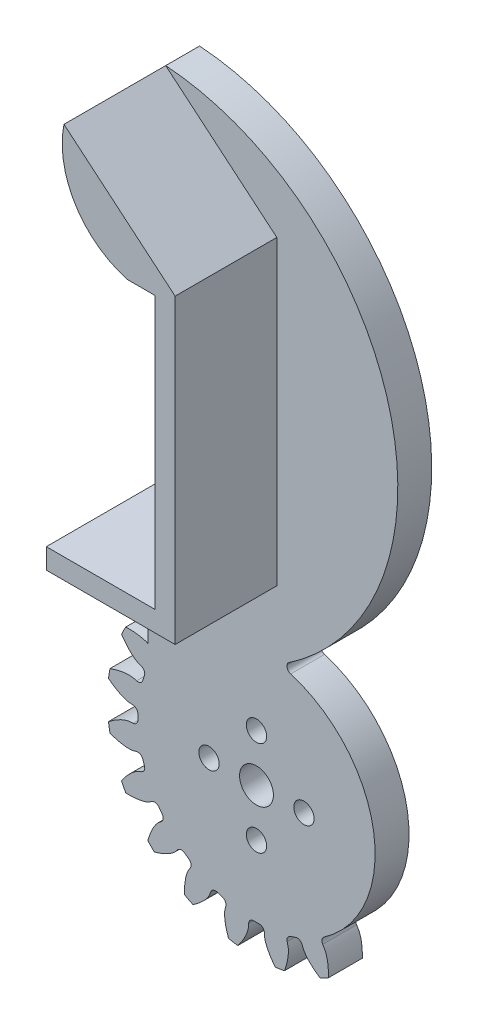
SolidWorks part; units mm, degrees
ref_plane "前视基准面" through (0, 0, 0) normal (0, 0, 1) x (1, 0, 0)
ref_plane "上视基准面" through (0, 0, 0) normal (0, 1, 0) x (1, 0, 0)
ref_plane "右视基准面" through (0, 0, 0) normal (1, 0, 0) x (0, 0, -1)
ref_axis "Axis1" through (0, 0, -88.99) along (0, 0, 1)
sketch "草图1" plane through (0, 0, 0) normal (0, 0, 1) x (1, 0, 0)
  circle A0 centre (0, 0) radius 22
extrude "LaShenA" add sketch "草图1" along normal blind 5
sketch "SketchA" plane through (0, 0, 5) normal (0, 0, 1) x (1, 0, 0)
  line L0 (0, 0) -> (0, 22) construction
  arc A0 (0.3853, 17.4958) -> (-0.3853, 17.4958) centre (0, 0) ccw
  arc A1 (3.5863, 22.7662) -> (-3.5863, 22.7662) centre (0, 0) ccw
  arc A2 (-0.3853, 17.4958) -> (-1.1606, 18.2089) centre (-0.4021, 18.2556) cw
  arc A3 (1.1606, 18.2089) -> (0.3853, 17.4958) centre (0.4021, 18.2556) cw
  circle A4 centre (0, 0) radius 18.7939 construction
  circle A5 centre (0, 0) radius 22 construction
  circle A6 centre (0, 0) radius 17.5 construction
  circle A7 centre (0, 0) radius 20 construction
  spline S0 degree 3 poles (1.1606, 18.2089) (1.1719, 18.3923) (1.1762, 18.6326) (1.2161, 18.8968) (1.2407, 19.0085) (1.2625, 19.0969) (1.2905, 19.1982) (1.3253, 19.3121) (1.3676, 19.4382) (1.4182, 19.5763) (1.4777, 19.7261) (1.5468, 19.887) (1.6261, 20.0586) (1.7163, 20.2406) (1.8179, 20.4325) (1.9317, 20.6337) (2.0581, 20.8437) (2.1978, 21.062) (2.3512, 21.288) (2.5189, 21.5211) (2.7014, 21.7607) (2.8992, 22.0061) (3.1899, 22.3474) (3.4232, 22.5992) (3.5863, 22.7662) knots 0.125068 0.125068 0.125068 0.125068 0.215847 0.244833 0.257593 0.272674 0.290074 0.309794 0.331834 0.356194 0.382875 0.411875 0.443195 0.476835 0.512796 0.551076 0.591676 0.634597 0.679837 0.727398 0.777278 0.829478 0.883999 1 1 1 1
  spline S1 degree 3 poles (-1.1606, 18.2089) (-1.1719, 18.3923) (-1.1762, 18.6326) (-1.2161, 18.8968) (-1.2407, 19.0085) (-1.2625, 19.0969) (-1.2905, 19.1982) (-1.3253, 19.3121) (-1.3676, 19.4382) (-1.4182, 19.5763) (-1.4777, 19.7261) (-1.5468, 19.887) (-1.6261, 20.0586) (-1.7163, 20.2406) (-1.8179, 20.4325) (-1.9317, 20.6337) (-2.0581, 20.8437) (-2.1978, 21.062) (-2.3512, 21.288) (-2.5189, 21.5211) (-2.7014, 21.7607) (-2.8992, 22.0061) (-3.1899, 22.3474) (-3.4232, 22.5992) (-3.5863, 22.7662) knots 0.125068 0.125068 0.125068 0.125068 0.215847 0.244833 0.257593 0.272674 0.290074 0.309794 0.331834 0.356194 0.382875 0.411875 0.443195 0.476835 0.512796 0.551076 0.591676 0.634597 0.679837 0.727398 0.777278 0.829478 0.883999 1 1 1 1
  dimension "D1" = 0.76
  dimension "Db" = 37.5877
  dimension "Da" = 44
  dimension "Df" = 35
  dimension "Dn" = 40
extrude "Cut-ExtrudeA" cut sketch "SketchA" against normal blind 50
pattern_circular "www.KYTool.cn" count 20 over 360 about axis through (0, 0, -88.99) along (0, 0, 1) of "Cut-ExtrudeA"
sketch "草图3" plane through (0, 0, 0) normal (0, 0, -1) x (-1, 0, 0)
  line L0 (16, 27) -> (16, 30)
  line L1 (16, 30) -> (0, 30)
  line L2 (0, 30) -> (0, 70.1)
  line L3 (0, 70.1) -> (15.3209, 82.9558) construction
  line L5 (13, 27) -> (-3, 27)
  line L6 (-3, 27) -> (-3, 71.4989)
  line L7 (-3, 71.4989) -> (13.3925, 85.2539)
  line L8 (0, 70.1) -> (4, 70.1)
  line L9 (13, 27) -> (16, 27)
  line L11 (13, 0) -> (13, 27) construction
  line L13 (16, 0) -> (16, 30) construction
  arc A1 (16, 0) -> (13, 9.3274) centre (0, 0) ccw construction
  arc A2 (4, 70.1) -> (13.3925, 85.2539) centre (0.6535, 82.6619) ccw
  arc A3 (13, 9.3274) -> (16, 0) centre (0, 0) ccw construction
  dimension "D2" = 32
  dimension "D10" = 13
  dimension "D3" = 30
  dimension "D4" = 16
  dimension "D5" = 40.1
  dimension "D6" = 130
  dimension "D7" = 20
  dimension "D9" = 4
  dimension "D8" = 3
extrude "凸台-拉伸2" add sketch "草图3" against normal blind 20 separate body contours L8 A2 L7 L6 L5 L9 L0 L1 L2
sketch "草图4" plane through (0, 0, 0) normal (0, 0, -1) x (-1, 0, 0)
  line L0 (16, 28.5) -> (16, 48.5) construction
  line L1 (16, 27) -> (16, 30) construction
  line L2 (16, 27) -> (16, 8.5864)
  line L3 (16, 8.5864) -> (11.9, 8.5864)
  line L4 (11.9, 8.5864) -> (11.9, 11.8826)
  line L5 (16, 27) -> (-3, 27) construction
  line L6 (-3, 27) -> (-3, 71.4989) construction
  line L7 (-3, 71.4989) -> (13.3925, 85.2539) construction
  line L8 (16, 27) -> (-3, 27)
  line L9 (-3, 27) -> (-3, 71.4989)
  line L10 (-3, 71.4989) -> (13.3925, 85.2539)
  arc A0 (13.3925, 85.2539) -> (11.9, 11.8826) centre (16, 48.5) ccw
  point P5 (13.3925, 85.2539)
  dimension "D1" = 20
extrude "凸台-拉伸3" add sketch "草图4" against normal blind 5
sketch "草图5" plane through (0, 0, 0) normal (0, 0, -1) x (-1, 0, 0)
  line L0 (17.5, 0) -> (8.5, 0) construction
  line L1 (-5.773, 16.5204) -> (-8.968, 20.5523)
  line L2 (-8.968, 20.5523) -> (-16.1954, 18.5363)
  line L3 (-16.1954, 18.5363) -> (-27.8925, -3.7928)
  line L4 (-27.8925, -3.7928) -> (-14.6739, -19.1987)
  line L5 (-14.6739, -19.1987) -> (-10.2862, -14.1578)
  line L6 (-5.5, 0) -> (-8.5, 0) construction
  line L7 (-2.5, 0) -> (-5.5, 0) construction
  line L8 (-8.5, 0) -> (-17.5, 0) construction
  line L9 (2.5, 0) -> (-2.5, 0) construction
  line L10 (5.5, 0) -> (2.5, 0) construction
  line L11 (8.5, 0) -> (5.5, 0) construction
  arc A0 (-17.4958, 0.3853) -> (-17.4958, -0.3853) centre (0, 0) ccw construction
  circle A1 centre (-7, 0) radius 1.5
  circle A2 centre (0, 7) radius 1.5
  circle A3 centre (7, 0) radius 1.5
  circle A4 centre (0, -7) radius 1.5
  circle A5 centre (0, 0) radius 2.5
  arc A6 (-5.773, 16.5204) -> (-10.2862, -14.1578) centre (0, 0) ccw
  arc A7 (-10.5955, -13.9279) -> (-9.972, -14.3809) centre (0, 0) ccw construction
  point P7 (0, 0)
  point P18 (0, 0)
  point P36 (0, 0)
  dimension "D1" = 7
  dimension "D2" = 3
  dimension "D4" = 5
  dimension "D3" = 4
extrude "切除-拉伸2" cut sketch "草图5" against normal blind 5
